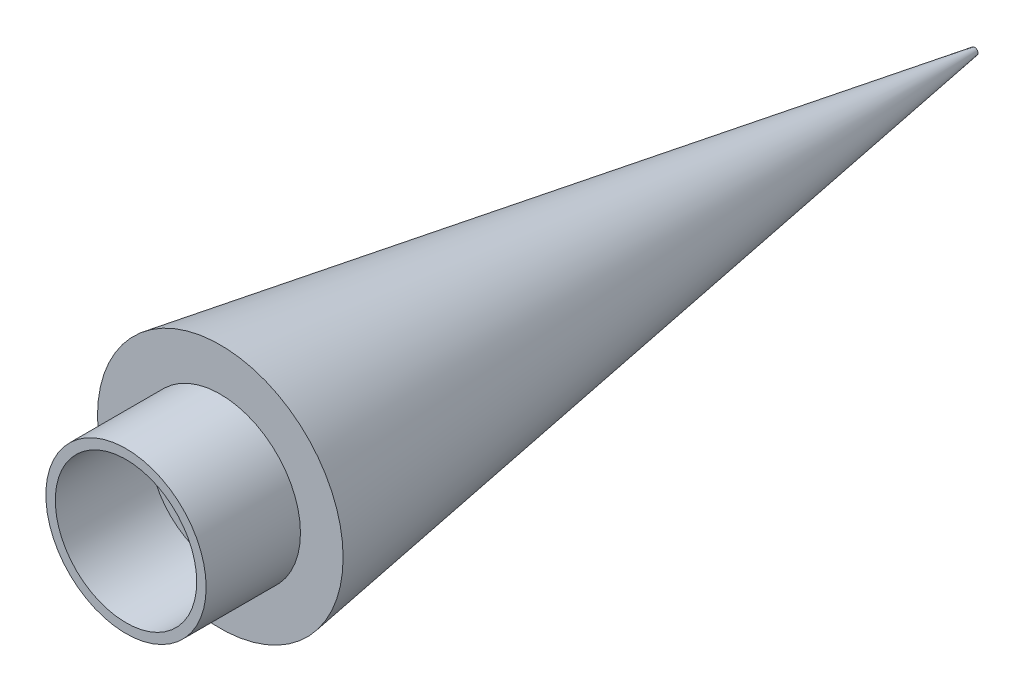
SolidWorks part; units mm, degrees
ref_plane "Front Plane" through (0, 0, 0) normal (0, 0, 1) x (1, 0, 0)
ref_plane "Top Plane" through (0, 0, 0) normal (0, 1, 0) x (1, 0, 0)
ref_plane "Right Plane" through (0, 0, 0) normal (1, 0, 0) x (0, 0, -1)
sketch "Sketch1" plane through (0, 0, 0) normal (0, 0, 1) x (1, 0, 0)
  circle A0 centre (0, 0) radius 7.5
  dimension "D1" = 15
extrude "Extrude-Thin1" add sketch "Sketch1" along normal blind 10 thin
sketch "Sketch2" plane through (0, 0, 0) normal (0, 0, -1) x (-1, 0, 0)
  circle A0 centre (0, 0) radius 13.0249
ref_plane "Plane1" through (0, 0, -40) normal (0, 0, 1) x (1, 0, 0)
sketch "Sketch3" plane through (0, 0, -40) normal (0, 0, 1) x (1, 0, 0)
  point P0 (0, 0)
extrude "Boss-Extrude1" add sketch "Sketch2" along normal blind 80 draft 9 contours A0
scale "Scale1" scale about origin uniform scaling yes scale factor 10
scale "Scale2" scale about origin uniform scaling yes scale factor 0.75
